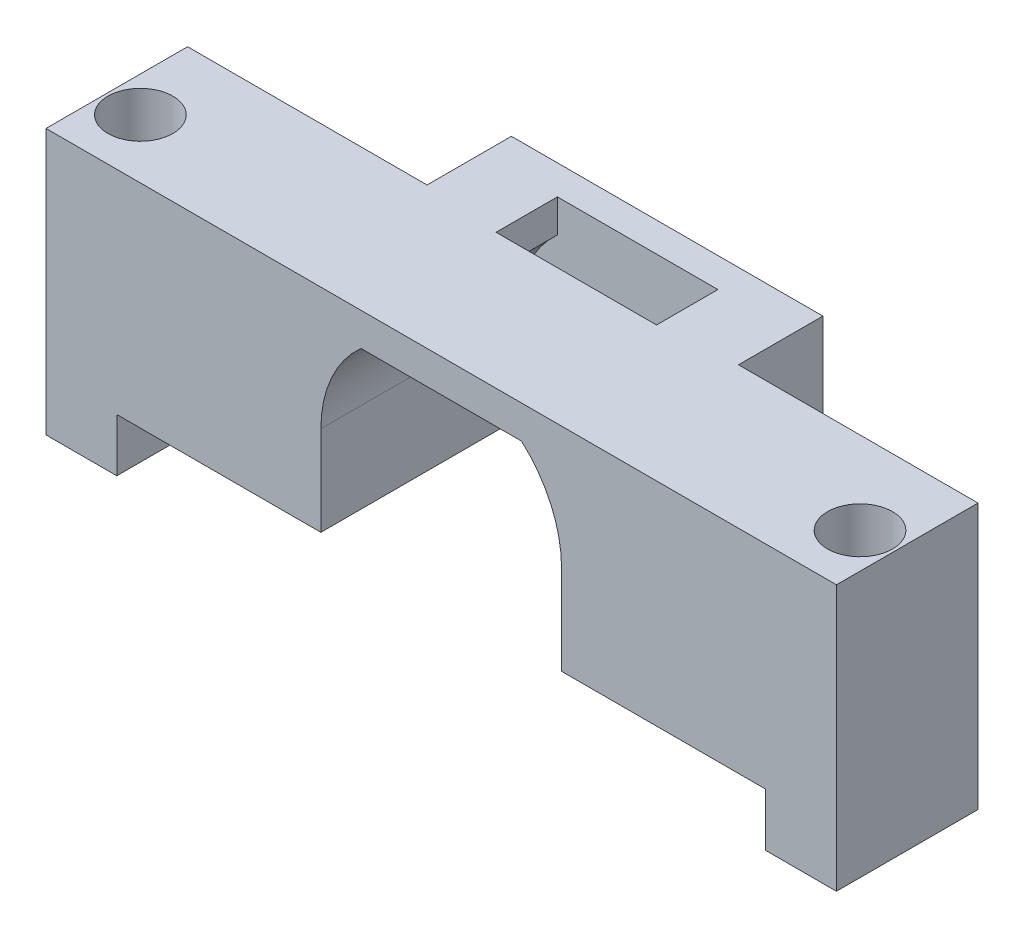
SolidWorks part; units mm, degrees
ref_plane "Front Plane" through (0, 0, 0) normal (0, 0, 1) x (1, 0, 0)
ref_plane "Top Plane" through (0, 0, 0) normal (0, 1, 0) x (1, 0, 0)
ref_plane "Right Plane" through (0, 0, 0) normal (1, 0, 0) x (0, 0, -1)
sketch "Sketch1" plane through (0, 0, 0) normal (0, 0, 1) x (1, 0, 0)
  line L0 (27.5, 0) -> (27.5, 18) construction
  line L1 (0, 0) -> (17.3, 0)
  line L2 (0, 0) -> (0, 18)
  line L3 (0, 18) -> (55, 18)
  line L4 (55, 0) -> (55, 18)
  line L5 (20.6971, 15.2) -> (34.3029, 15.2)
  line L7 (17.3, 0) -> (17.3, 7.6)
  line L8 (37.7, 0) -> (37.7, 7.6)
  line L9 (20.6971, 15.2) -> (34.3029, 15.2)
  line L10 (17.3, 0) -> (37.7, 15.2) construction
  line L11 (17.3, 15.2) -> (37.7, 0) construction
  line L12 (0, 15.2) -> (55, 15.2) construction
  line L13 (37.7, 0) -> (55, 0)
  line L14 (0, 0) -> (55, 0) construction
  line L15 (17.3, 7.6) -> (17.3, 15.2)
  line L16 (17.3, 15.2) -> (37.7, 15.2)
  line L17 (37.7, 15.2) -> (37.7, 7.6)
  arc A2 (20.6971, 15.2) -> (17.3, 7.6) centre (27.5, 7.6) ccw
  arc A3 (37.7, 7.6) -> (34.3029, 15.2) centre (27.5, 7.6) ccw
  dimension "D3" = 10.2
  dimension "D6" = 20.4
  dimension "D1" = 55
  dimension "D2" = 18
  dimension "D5" = 10.2
  dimension "D4" = 15.2
extrude "Boss-Extrude2" add sketch "Sketch1" along normal blind 12 contours L16 L17 L8 L13 L4 L3 L2 L1 L7 L15 L5 | A2 L16 L15 | A3 L17 L16
sketch "Sketch2" plane through (0, 0, 0) normal (-1, 0, 0) x (0, 0, 1)
  line L0 (12, 0) -> (12, 18) construction
  line L5 (12, 0) -> (0, 0) construction
  line L6 (0, 18) -> (12, 18)
  line L7 (0, 18) -> (0, -4.5)
  line L8 (0, -4.5) -> (12, -4.5)
  line L9 (12, 18) -> (12, -4.5)
  dimension "D1" = 4.5
extrude "Boss-Extrude3" add sketch "Sketch2" along normal blind 6
sketch "Sketch3" plane through (55, 0, 0) normal (1, 0, 0) x (0, 0, -1)
  line L1 (-12, 18) -> (0, 18)
  line L2 (-12, 18) -> (-12, -4.5)
  line L3 (-12, -4.5) -> (0, -4.5)
  line L4 (0, 18) -> (0, -4.5)
extrude "Boss-Extrude4" add sketch "Sketch3" along normal blind 6
sketch "Sketch4" plane through (0, 18, 0) normal (0, 1, 0) x (1, 0, 0)
  line L0 (0, 0) -> (0, -12) construction
  line L1 (-6, -12) -> (-6, 0) construction
  line L3 (27.5, 0) -> (27.5, -12) construction
  line L4 (-6, 0) -> (61, 0) construction
  line L5 (-6, -12) -> (61, -12) construction
  line L6 (0, 0) -> (0, -12) construction
  circle A0 centre (-3, -7) radius 1.75
  circle A1 centre (58, -7) radius 1.75
  dimension "D1" = 3.5
  dimension "D2" = 3
  dimension "D3" = 5
extrude "Cut-Extrude1" cut sketch "Sketch4" against normal up to surface (22.5 mm away) up to face at (-3, -4.5, 6)
sketch "Sketch5" plane through (0, 0, 0) normal (0, 0, -1) x (-1, 0, 0)
  line L0 (-37.7, 7.6) -> (-17.3, 7.6) construction
  line L1 (-37.7, 0) -> (-40.7, 0)
  line L2 (-37.7, 0) -> (-55, 0) construction
  line L3 (-40.7, 0) -> (-40.7, 18)
  line L4 (6, 18) -> (-61, 18) construction
  line L5 (-40.7, 18) -> (-14.3, 18)
  line L6 (-27.5, 18) -> (-27.5, 0) construction
  line L7 (-17.3, 6) -> (-17.3, 0)
  line L8 (-20.6971, 15.2) -> (-34.3029, 15.2) construction
  line L9 (-37.7, 7.6) -> (-37.7, 0) construction
  line L10 (-20.6971, 15.2) -> (-34.3029, 15.2)
  line L11 (-37.7, 6) -> (-37.7, 0)
  line L12 (-14.3, 0) -> (-14.3, 18)
  line L13 (-17.3, 0) -> (-14.3, 0)
  arc A0 (-37.7, 6) -> (-37.5745, 6.0049) centre (-37.7, 7.6) ccw
  arc A1 (-34.3029, 15.2) -> (-37.7, 7.6) centre (-27.5, 7.6) ccw construction
  arc A2 (-34.3029, 15.2) -> (-37.5745, 9.1951) centre (-27.5, 7.6) ccw
  arc A3 (-20.6971, 15.2) -> (-17.4255, 9.1951) centre (-27.5, 7.6) cw
  arc A4 (-17.3, 6) -> (-17.4255, 6.0049) centre (-17.3, 7.6) cw
  arc A5 (-17.4255, 6.0049) -> (-20.6971, 15.2) centre (-27.5, 7.6) ccw
  arc A6 (-34.3029, 15.2) -> (-37.5745, 6.0049) centre (-27.5, 7.6) ccw
  point P22 (-27.5, 15.2)
  dimension "D1" = 3.2
  dimension "D2" = 3
extrude "Boss-Extrude5" add sketch "Sketch5" along normal blind 4.65
sketch "Sketch6" plane through (0, 0, -4.65) normal (0, 0, -1) x (-1, 0, 0)
  line L0 (-27.5, 18) -> (-27.5, 0) construction
  line L1 (-14.3, 18) -> (-40.7, 18) construction
  line L2 (-36.1012, 7.5372) -> (-18.8988, 7.5372) construction
  line L3 (-40.7, 18) -> (-40.7, 0)
  line L4 (-40.7, 0) -> (-37.7, 0) construction
  line L5 (-40.7, 18) -> (-40.7, 0) construction
  line L6 (-40.7, 0) -> (-14.3, 0)
  line L7 (-17.3, 0) -> (-14.3, 0) construction
  line L8 (-14.3, 0) -> (-14.3, 18)
  line L9 (-14.3, 18) -> (-40.7, 18)
  arc A0 (-37.7, 6) -> (-37.5745, 9.1951) centre (-37.7, 7.6) ccw construction
  arc A1 (-17.4255, 9.1951) -> (-17.3, 6) centre (-17.3, 7.6) ccw construction
  circle A2 centre (-27.5, 7.5372) radius 4.925
  dimension "D1" = 9.85
extrude "Boss-Extrude6" add sketch "Sketch6" along normal blind 2.5
sketch "Sketch7" plane through (0, 18, 0) normal (0, 1, 0) x (1, 0, 0)
  circle A0 centre (-3, -7) radius 2.75
  circle A1 centre (58, -7) radius 2.75
  dimension "D1" = 5.5
  dimension "D2" = 5.5
extrude "Cut-Extrude2" cut sketch "Sketch7" against normal blind 15
sketch "Sketch12" plane through (0, 0, -7.15) normal (0, 0, -1) x (-1, 0, 0)
  line L0 (-40.7, 0) -> (-14.3, 0) construction
  line L1 (-22.5946, 7.0978) -> (-32.425, 7.0978)
  line L2 (-22.5946, 7.0978) -> (-22.5946, 0)
  line L3 (-22.5946, 0) -> (-32.425, 0)
  line L4 (-32.425, 7.0978) -> (-32.425, 0)
  circle A0 centre (-27.5, 7.5372) radius 4.925 construction
extrude "Cut-Extrude12" cut sketch "Sketch12" against normal up to surface (2.5 mm away)
sketch "Sketch13" plane through (0, 0, 0) normal (0, 0, 1) x (1, 0, 0)
  line L0 (17.3, 7.6) -> (17.3, 6) construction
  line L1 (37.7, 6) -> (37.7, 7.6) construction
  line L2 (17.3, 7.6) -> (17.3, 6)
  line L3 (37.7, 6) -> (37.7, 7.6)
  arc A0 (17.3, 6) -> (17.4255, 9.1951) centre (17.3, 7.6) ccw construction
  arc A1 (17.4255, 9.1951) -> (17.3, 7.6) centre (27.5, 7.6) ccw construction
  arc A2 (37.7, 7.6) -> (37.5745, 9.1951) centre (27.5, 7.6) ccw construction
  arc A3 (37.5745, 9.1951) -> (37.7, 6) centre (37.7, 7.6) ccw construction
  arc A4 (17.3, 6) -> (17.4255, 9.1951) centre (17.3, 7.6) ccw
  arc A5 (17.4255, 9.1951) -> (17.3, 7.6) centre (27.5, 7.6) ccw
  arc A6 (37.7, 7.6) -> (37.5745, 9.1951) centre (27.5, 7.6) ccw
  arc A7 (37.5745, 9.1951) -> (37.7, 6) centre (37.7, 7.6) ccw
extrude "Cut-Extrude13" cut sketch "Sketch13" against normal up to surface (4.65 mm away)
sketch "Sketch14" plane through (0, 15.2, 0) normal (0, -1, 0) x (-1, 0, 0)
  line L0 (-34.3029, -12) -> (-34.3029, 4.65) construction
  line L1 (-34.3029, -0.55) -> (-20.6971, -0.55)
  line L2 (-34.3029, -0.55) -> (-34.3029, 4.65)
  line L3 (-34.3029, 4.65) -> (-20.6971, 4.65)
  line L4 (-20.6971, -0.55) -> (-20.6971, 4.65)
  dimension "D1" = 5.2
extrude "Cut-Extrude14" cut sketch "Sketch14" against normal up to surface (2.8 mm away) contours L2 L1 L4 L3
